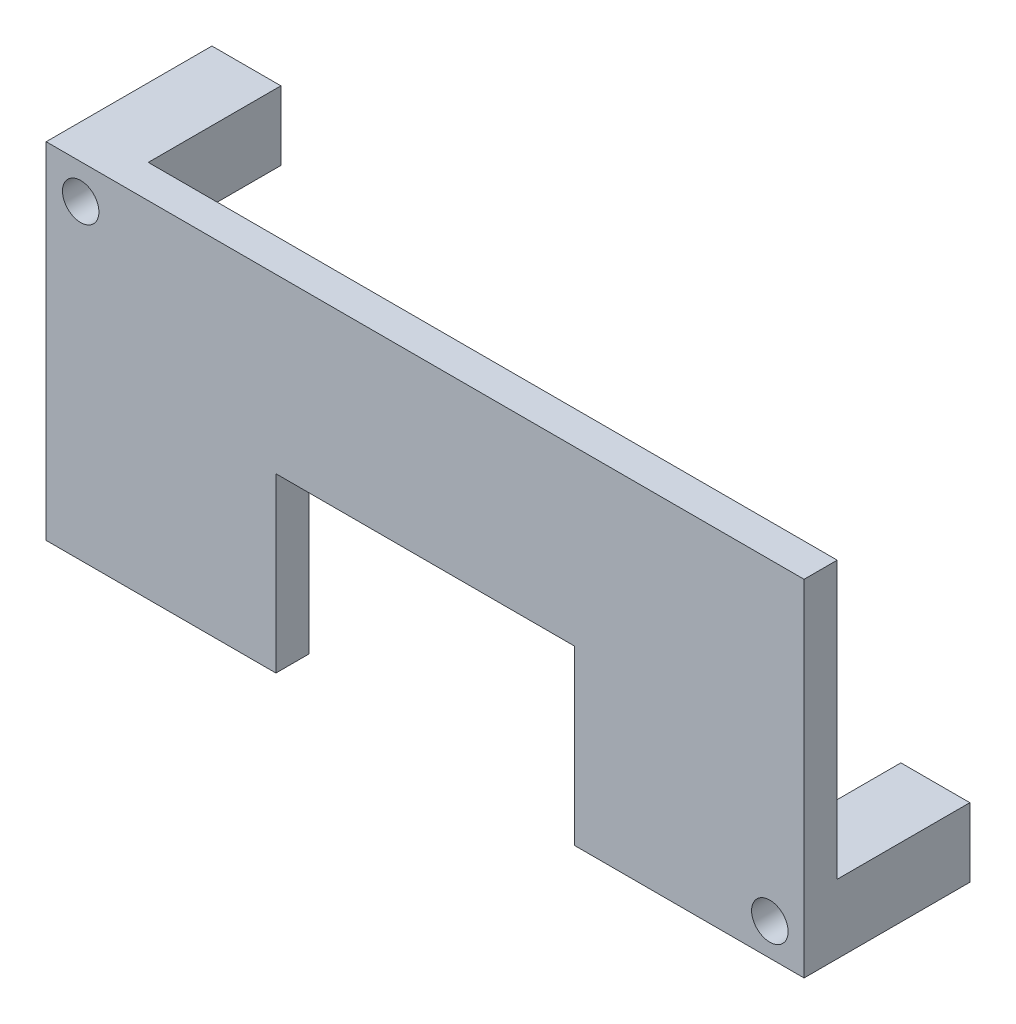
SolidWorks part; units mm, degrees
ref_plane "Front" through (0, 0, 0) normal (0, 0, 1) x (1, 0, 0)
ref_plane "Top" through (0, 0, 0) normal (0, 1, 0) x (1, 0, 0)
ref_plane "Right" through (0, 0, 0) normal (1, 0, 0) x (0, 0, -1)
sketch "Skizze1" plane through (0, 0, 0) normal (0, 0, 1) x (1, 0, 0)
  line L1 (-22.86, -10.415) -> (22.86, -10.415)
  line L2 (-22.86, -10.415) -> (-22.86, 10.415)
  line L3 (-22.86, 10.415) -> (22.86, 10.415)
  line L4 (22.86, -10.415) -> (22.86, 10.415)
  line L5 (-22.86, -10.415) -> (22.86, 10.415) construction
  line L6 (-22.86, 10.415) -> (22.86, -10.415) construction
  point P1 (0, 0)
  dimension "D1" = 45.72
  dimension "D2" = 20.83
extrude "Aufsatz-Linear austragen1" add sketch "Skizze1" along normal blind 2
sketch "Skizze3" plane through (0, 0, 0) normal (0, 0, -1) x (-1, 0, 0)
  line L0 (0, 0) -> (0, -10.415) construction
  line L1 (22.86, -10.415) -> (-22.86, -10.415) construction
  line L3 (9, 0) -> (-9, 0)
  line L4 (9, 0) -> (9, -10.415)
  line L5 (9, -10.415) -> (-9, -10.415)
  line L6 (-9, 0) -> (-9, -10.415)
  line L7 (9, 0) -> (-9, -10.415) construction
  line L8 (9, -10.415) -> (-9, 0) construction
  point P5 (0, -5.2075)
  dimension "D1" = 18
  dimension "D2" = 10.415
extrude "Schnitt-Linear austragen1" cut sketch "Skizze3" against normal blind 10
ref_plane "Ebene1" through (-22.86, 10.415, 2) normal (0, -1, 0) x (-1, 0, 0)
sketch "Skizze7" plane through (0, 0, 0) normal (0, 0, -1) x (-1, 0, 0)
  line L1 (22.86, 10.415) -> (18.7, 10.415)
  line L2 (22.86, 10.415) -> (22.86, 6.255)
  line L3 (22.86, 6.255) -> (18.7, 6.255)
  line L4 (18.7, 10.415) -> (18.7, 6.255)
  line L5 (-18.7, -6.255) -> (-22.86, -6.255)
  line L6 (-18.7, -6.255) -> (-18.7, -10.415)
  line L7 (-18.7, -10.415) -> (-22.86, -10.415)
  line L8 (-22.86, -6.255) -> (-22.86, -10.415)
  dimension "D1" = 4.16
  dimension "D2" = 4.16
  dimension "D3" = 4.16
  dimension "D4" = 4.16
extrude "Aufsatz-Linear austragen2" add sketch "Skizze7" along normal blind 8
hole_wizard "Durchgangsloch für M21" positions "Skizze10" profile "Skizze9" hole size "M2" standard "DIN" end condition through all
sketch "Skizze10" plane through (0, 0, -8) normal (0, 0, -1) x (-1, 0, 0)
  point P0 (-20.7955, -8.4767)
  point P2 (20.7772, 8.3322)
sketch "Skizze9" plane through (20.7955, -8.4767, -8) normal (1, 0, 0) x (0, 1, 0)
  line L0 (0, 0) -> (0, 10)
  line L1 (0, 10) -> (1.1, 10)
  line L2 (1.1, 10) -> (1.1, 0)
  line L5 (1.1, 0) -> (0, 0)
  line L11 (0, -6.35) -> (0, 107.95) construction
  dimension "Bohrerdurchmesser" = 2.2
  dimension "Bohrungstiefe" = 10
